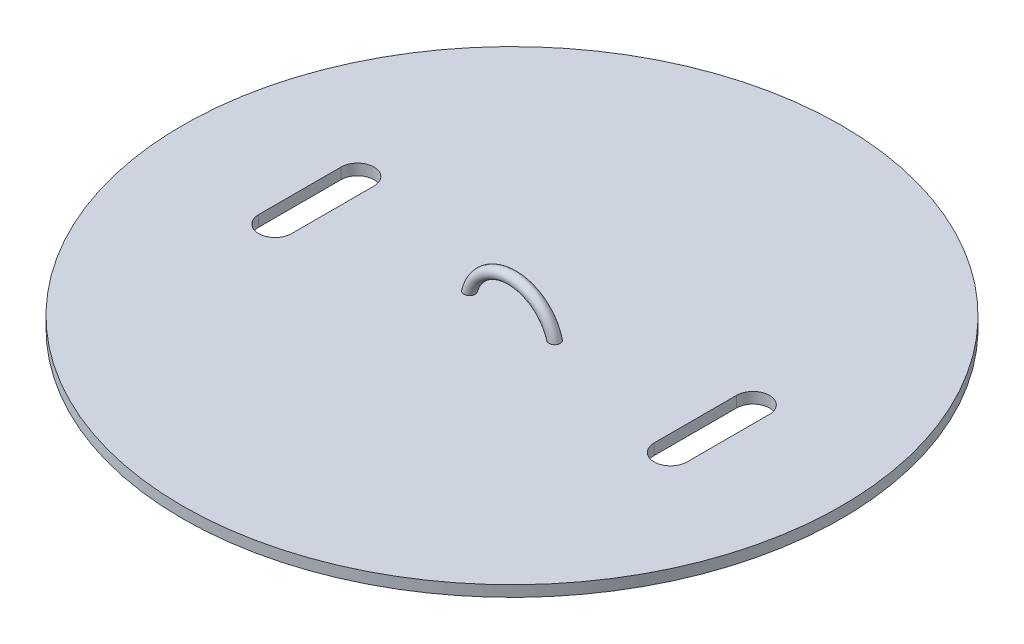
SolidWorks part; units mm, degrees
material "ABS PC"
ref_plane "Front Plane" through (0, 0, 0) normal (0, 0, 1) x (1, 0, 0)
ref_plane "Top Plane" through (0, 0, 0) normal (0, 1, 0) x (1, 0, 0)
ref_plane "Right Plane" through (0, 0, 0) normal (1, 0, 0) x (0, 0, -1)
sketch "Sketch1" plane through (0, 0, 0) normal (0, 1, 0) x (1, 0, 0)
  circle A0 centre (0, -137.726) radius 60
  dimension "D1" = 120
extrude "Boss-Extrude1" add sketch "Sketch1" along normal blind 2 contours A0
sketch "Sketch3" plane through (0, 0, 0) normal (0, 1, 0) x (1, 0, 0)
  line L0 (0, -77.726) -> (0, -197.726) construction
  circle A0 centre (8, -137.726) radius 1
  circle A1 centre (0, -137.726) radius 60 construction
  point P2 (0, -137.726)
  dimension "D1" = 2
  dimension "D2" = 8
revolve "Revolve1" add sketch "Sketch3" angle 180 about L0
sketch "Sketch4" plane through (0, 2, 0) normal (0, 1, 0) x (1, 0, 0)
  line L0 (36, -129.8501) -> (36, -144.8501) construction
  line L1 (39, -129.8501) -> (39, -144.8501)
  line L2 (33, -129.8501) -> (33, -144.8501)
  line L4 (-0.0012, -137.3501) -> (59.9988, -137.3501) construction
  line L5 (59.9988, -137.3501) -> (-62.481, -137.3501) construction
  line L6 (0, -4.95) -> (0, 4.95) construction
  line L7 (-36, -129.8501) -> (-36, -144.8501) construction
  line L8 (-39, -129.8501) -> (-39, -144.8501)
  line L9 (-33, -129.8501) -> (-33, -144.8501)
  arc A0 (39, -129.8501) -> (33, -129.8501) centre (36, -129.8501) ccw
  arc A1 (33, -144.8501) -> (39, -144.8501) centre (36, -144.8501) ccw
  circle A3 centre (0, -137.726) radius 60 construction
  arc A4 (-39, -129.8501) -> (-33, -129.8501) centre (-36, -129.8501) cw
  arc A5 (-33, -144.8501) -> (-39, -144.8501) centre (-36, -144.8501) cw
  point P2 (36, -137.3501)
  point P7 (0, 0)
  point P16 (-36, -137.3501)
  dimension "D1" = 6
  dimension "D2" = 15
extrude "Cut-Extrude1" cut sketch "Sketch4" against normal blind 10
